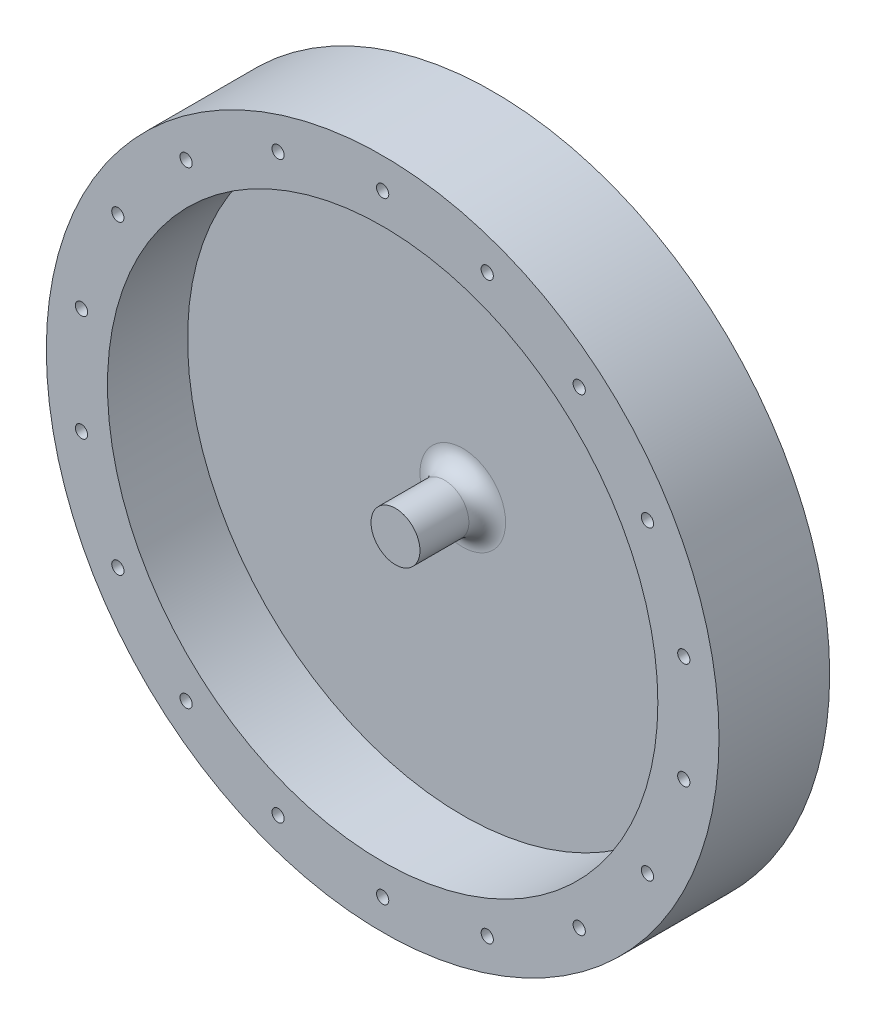
SolidWorks part; units mm, degrees
material "7075-T6 (SN)"
ref_plane "Front Plane" through (0, 0, 0) normal (0, 0, 1) x (1, 0, 0)
ref_plane "Top Plane" through (0, 0, 0) normal (0, 1, 0) x (1, 0, 0)
ref_plane "Right Plane" through (0, 0, 0) normal (1, 0, 0) x (0, 0, -1)
sketch "Sketch1" plane through (0, 0, 0) normal (0, 0, 1) x (1, 0, 0)
  circle A0 centre (0, 0) radius 2
  circle A1 centre (0, 0) radius 4
  dimension "D1" = 4
  dimension "D2" = 8
extrude "Boss-Extrude1" add sketch "Sketch1" along normal mid plane 16
sketch "Sketch2" plane through (0, 0, 0) normal (0, 0, 1) x (1, 0, 0)
  circle A0 centre (0, 0) radius 4
  circle A1 centre (0, 0) radius 45
  dimension "D1" = 41
extrude "Boss-Extrude2" add sketch "Sketch2" along normal blind 5 from surface at -8 starting at face at (4, 0, -8)
sketch "Sketch3" plane through (0, 0, 0) normal (0, 0, 1) x (1, 0, 0)
  circle A0 centre (0, 0) radius 45
  circle A1 centre (0, 0) radius 55
  circle A2 centre (0, 0) radius 45 construction
  dimension "D1" = 10
extrude "Boss-Extrude3" add sketch "Sketch3" along normal blind 18.1 from surface at -8 starting at face at (2, 0, -8)
sketch "Sketch4" plane through (0, 0, 8) normal (0, 0, 1) x (1, 0, 0)
  circle A0 centre (0, 0) radius 2
extrude "Boss-Extrude4" add sketch "Sketch4" against normal blind 2
sketch "Sketch5" plane through (0, 0, 10.1) normal (0, 0, 1) x (1, 0, 0)
  line L0 (0, 0) -> (0, 86.4234) construction
  circle A0 centre (0, 0) radius 50 construction
  circle A1 centre (0, 0) radius 55 construction
  circle A2 centre (0, 50) radius 1
  dimension "D1" = 5
  dimension "D2" = 2
extrude "Cut-Extrude1" cut sketch "Sketch5" against normal blind 5
pattern_circular "CirPattern1" count 18 over 360 about axis through (0, 0, 0) along (0, 0, 1) of "Cut-Extrude1"
ref_plane "Plane1" through (0, 0, 1.05) normal (0, 0, 1) x (1, 0, 0)
mirror "Mirror1" about plane through (0, 0, 1.05) normal (0, 0, 1) of "CirPattern1", "Cut-Extrude1"
sketch "Sketch6" plane through (0, 0, 0) normal (1, 0, 0) x (0, 0, -1)
  line L0 (-25.0808, 0) -> (28.497, 0) construction
chamfer "Chamfer1" distance 0.5 angle 45 1 edges at (2, 0, -8)
fillet "Fillet1" radius 3 1 edges at (4, 0, -3)
